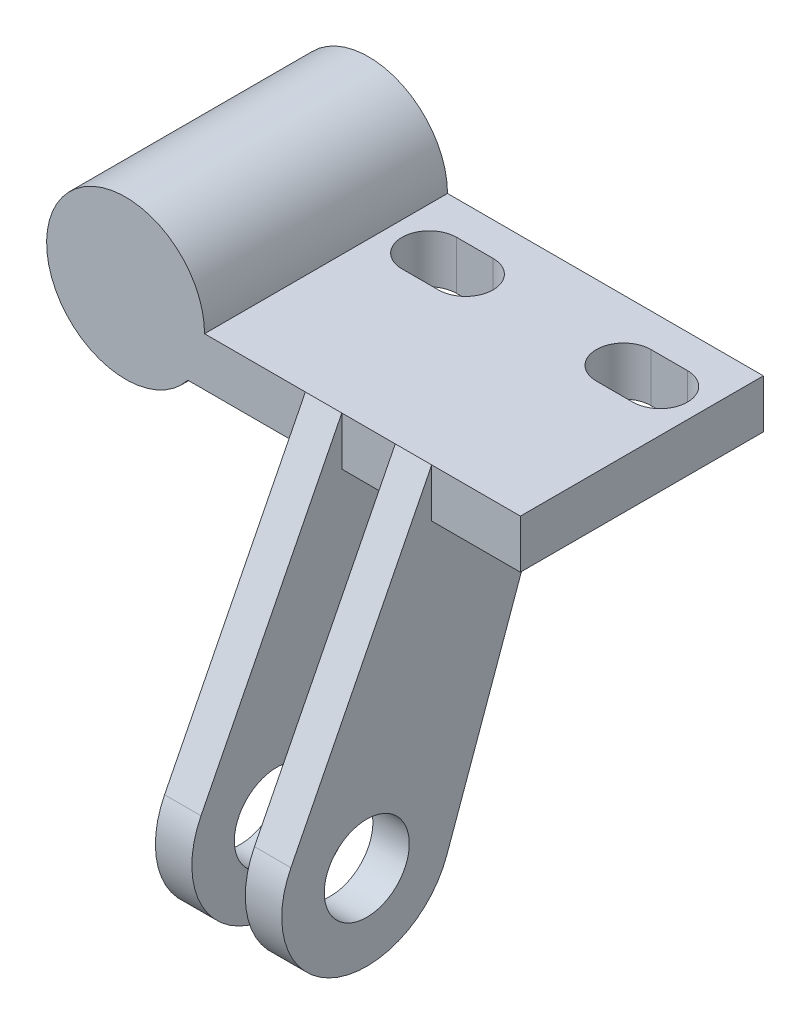
SolidWorks part; units mm, degrees
ref_plane "Спереди" through (0, 0, 0) normal (0, 0, 1) x (1, 0, 0)
ref_plane "Сверху" through (0, 0, 0) normal (0, 1, 0) x (1, 0, 0)
ref_plane "Справа" through (0, 0, 0) normal (1, 0, 0) x (0, 0, -1)
other "Configuration Table"
sketch "Эскиз1" plane through (0, 0, 0) normal (0, 0, 1) x (1, 0, 0)
  line L0 (5.1235, -4) -> (32.5, -4)
  line L1 (32.5, -4) -> (32.5, 0)
  line L2 (32.5, 0) -> (6.5, 0)
  circle A0 centre (0, 0) radius 4.1
  arc A1 (6.5, 0) -> (5.1235, -4) centre (0, 0) ccw
  circle A2 centre (39, 0) radius 6.5 construction
  dimension "D1" = 8.2
  dimension "D2" = 13
  dimension "D3" = 26
  dimension "D7" = 13
  dimension "D4" = 4
  dimension "D5" = 6.5
  dimension "D6" = 32.5
extrude "Бобышка-Вытянуть1" add sketch "Эскиз1" along normal blind 20
sketch "Эскиз2" plane through (0, 0, 20) normal (0, 0, 1) x (1, 0, 0)
  circle A0 centre (0, 0) radius 4.9232
extrude "Бобышка-Вытянуть2" add sketch "Эскиз2" against normal blind 3
sketch "Эскиз3" plane through (0, 0, 0) normal (0, 1, 0) x (1, 0, 0)
  line L0 (10, -7.25) -> (13, -7.25)
  line L1 (10, -2.75) -> (13, -2.75)
  line L6 (26, -2.75) -> (29, -2.75)
  line L7 (26, -7.25) -> (29, -7.25)
  line L8 (32.5, -20) -> (6.5, -20) construction
  line L9 (6.5, -20) -> (6.5, 0) construction
  line L11 (32.5, -20) -> (32.5, 0) construction
  arc A4 (10, -2.75) -> (10, -7.25) centre (10, -5) ccw
  arc A5 (29, -7.25) -> (29, -2.75) centre (29, -5) ccw
  arc A6 (13, -7.25) -> (13, -2.75) centre (13, -5) ccw
  arc A7 (26, -2.75) -> (26, -7.25) centre (26, -5) ccw
  dimension "D1" = 4.5
  dimension "D2" = 4.5
  dimension "D3" = 15
  dimension "D5" = 15
  dimension "D7" = 4.5
  dimension "D8" = 4.5
  dimension "D4" = 3.5
  dimension "D6" = 3.5
  dimension "D9" = 3
  dimension "D10" = 3
extrude "Вырез-Вытянуть1" cut sketch "Эскиз3" against normal blind 13
ref_plane "Плоскость1" through (22.2, 0, 0) normal (1, 0, 0) x (0, 0, -1)
sketch "Эскиз6" plane through (22.2, 0, 0) normal (1, 0, 0) x (0, 0, -1)
  line L7 (-31.592, -22.9186) -> (-20, 0)
  line L8 (-20, 0) -> (-10, -4)
  line L9 (-10, -4) -> (-18.7557, -28.4389)
  line L10 (-20, -4) -> (0, -4) construction
  line L11 (-20, 6.5) -> (-20, -6.5) construction
  line L14 (-17, -4) -> (203, -4) construction
  circle A2 centre (-25.3456, -26.078) radius 3.5
  arc A3 (-18.7557, -28.4389) -> (-31.592, -22.9186) centre (-25.3456, -26.078) cw
  dimension "D1" = 7
  dimension "D2" = 7
  dimension "D3" = 109.711
  dimension "D4" = 153.17
  dimension "D5" = 26.8872
extrude "Бобышка-Вытянуть3" add sketch "Эскиз6" along normal blind 3
ref_plane "Плоскость2" through (20, 0, 0) normal (1, 0, 0) x (0, 0, -1)
mirror "Зеркальное отражение1" about plane through (20, 0, 0) normal (1, 0, 0) of "Бобышка-Вытянуть3"
